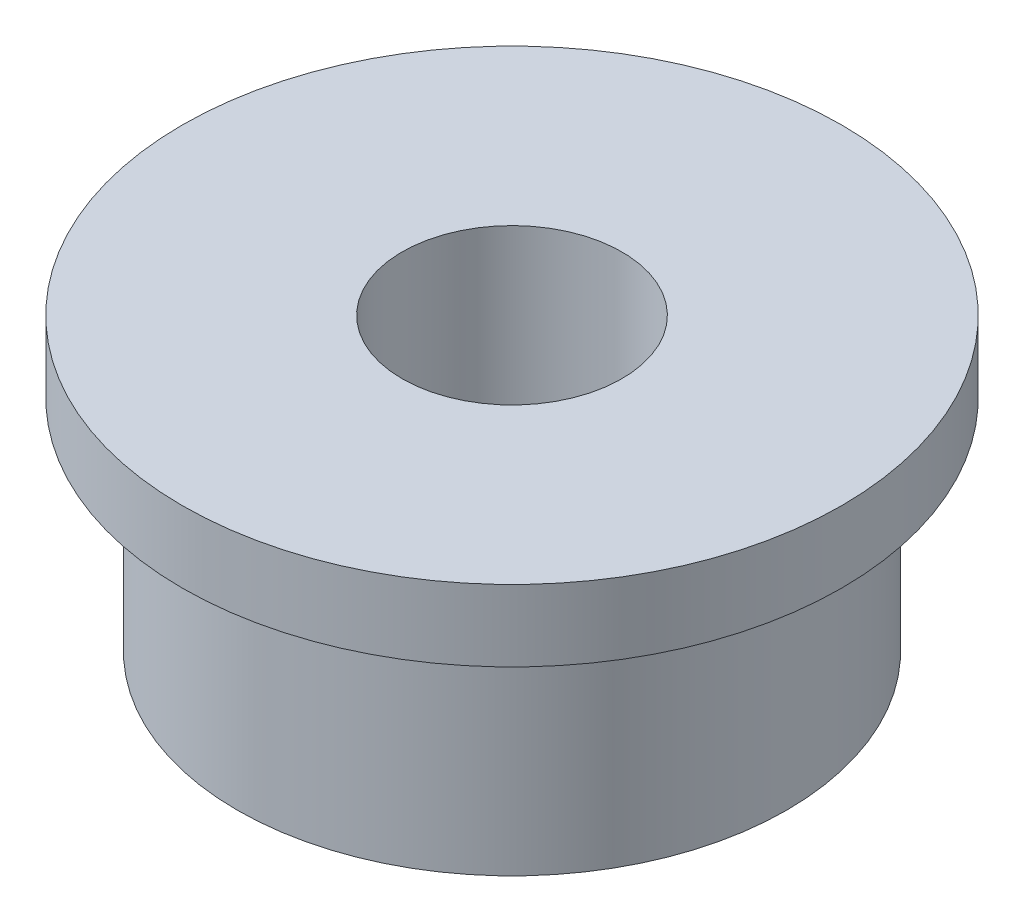
SolidWorks part; units mm, degrees
ref_plane "Front Plane" through (0, 0, 0) normal (0, 0, 1) x (1, 0, 0)
ref_plane "Top Plane" through (0, 0, 0) normal (0, 1, 0) x (1, 0, 0)
ref_plane "Right Plane" through (0, 0, 0) normal (1, 0, 0) x (0, 0, -1)
sketch "Sketch1" plane through (0, 0, 0) normal (0, 1, 0) x (1, 0, 0)
  circle A0 centre (0, 0) radius 2.5
  circle A1 centre (0, 0) radius 1
  dimension "D1" = 5
  dimension "D2" = 2
extrude "Boss-Extrude1" add sketch "Sketch1" along normal blind 2
sketch "Sketch2" plane through (0, 2, 0) normal (0, 1, 0) x (1, 0, 0)
  circle A0 centre (0, 0) radius 1
  circle A1 centre (0, 0) radius 3
  dimension "D1" = 6
extrude "Boss-Extrude2" add sketch "Sketch2" along normal blind 0.65
